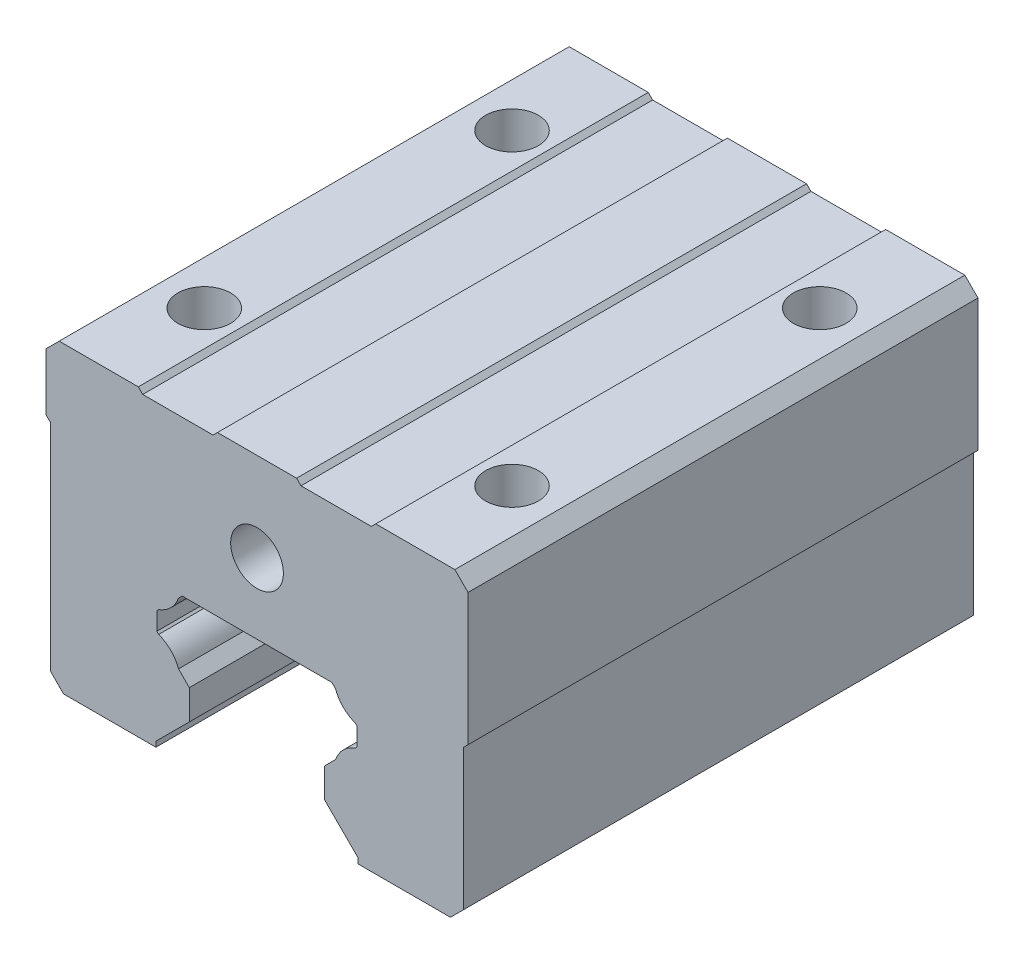
SolidWorks part; units mm, degrees
material "合金鋼"
ref_plane "Front Plane" through (0, 0, 0) normal (0, 0, 1) x (1, 0, 0)
ref_plane "Top Plane" through (0, 0, 0) normal (0, 1, 0) x (1, 0, 0)
ref_plane "Right Plane" through (0, 0, 0) normal (1, 0, 0) x (0, 0, -1)
sketch "Sketch2" plane through (0, 0, 0) normal (0, 0, 1) x (1, 0, 0)
  line L0 (22, 0) -> (23.5, 1.5)
  line L1 (23.5, 1.5) -> (23.5, 17.5)
  line L2 (23.5, 17.5) -> (24, 18)
  line L3 (24, 18) -> (24, 33)
  line L4 (24, 33) -> (22.5, 34.5)
  line L5 (22.5, 34.5) -> (13.5, 34.5)
  line L6 (13.5, 34.5) -> (13, 34)
  line L7 (13, 34) -> (5, 34)
  line L8 (5, 34) -> (4.5, 34.5)
  line L9 (4.5, 34.5) -> (-4.5, 34.5)
  line L10 (-4.5, 34.5) -> (-5, 34)
  line L11 (-5, 34) -> (-13, 34)
  line L12 (-13, 34) -> (-13.5, 34.5)
  line L13 (-13.5, 34.5) -> (-22.5, 34.5)
  line L14 (-22.5, 34.5) -> (-24, 33)
  line L15 (-24, 33) -> (-24, 26.5)
  line L16 (-24, 26.5) -> (-23.5, 26)
  line L17 (-23.5, 26) -> (-23.5, 1.5)
  line L18 (-23.5, 1.5) -> (-22, 0)
  line L19 (-7.7, 4.3937) -> (-11.5, 0.6)
  line L20 (-22, 0) -> (-11.5, 0)
  line L21 (11.5, 0) -> (22, 0)
  line L22 (-11.5, 0.6) -> (-11.5, 0)
  line L23 (7.7, 4.3937) -> (11.5, 0.6)
  line L24 (-7.7, 4.3937) -> (-7.7, 7.7737)
  line L25 (-7.7, 7.7737) -> (-8.93, 9.0057)
  line L26 (-11.1862, 11.2657) -> (-11.3959, 11.4757)
  line L27 (-11.3959, 11.4757) -> (-11.3959, 13.5057)
  line L28 (-11.3959, 13.5057) -> (-11.1862, 13.7157)
  line L29 (-8.93, 15.9757) -> (-8.5207, 16.3857)
  line L30 (-8.5207, 16.3857) -> (8.5207, 16.3857)
  line L31 (8.5207, 16.3857) -> (8.93, 15.9757)
  line L32 (11.1862, 13.7157) -> (11.3959, 13.5057)
  line L33 (11.3959, 13.5057) -> (11.3959, 11.4757)
  line L34 (11.3959, 11.4757) -> (11.1862, 11.2657)
  line L35 (8.93, 9.0057) -> (7.7, 7.7737)
  line L36 (7.7, 7.7737) -> (7.7, 4.3937)
  line L37 (11.5, 0.6) -> (11.5, 0)
  arc A0 (-8.93, 9.0057) -> (-11.1862, 11.2657) centre (-12.4594, 7.7384) ccw
  arc A1 (-11.1862, 13.7157) -> (-8.93, 15.9757) centre (-12.4594, 17.243) ccw
  arc A2 (8.93, 15.9757) -> (11.1862, 13.7157) centre (12.4594, 17.243) ccw
  arc A3 (11.1862, 11.2657) -> (8.93, 9.0057) centre (12.4594, 7.7384) ccw
  dimension "D10" = 1.5
  dimension "D9" = 3.8
  dimension "D28" = 34
  dimension "D11" = 0.6
  dimension "D19" = 2.26
  dimension "D1" = 34.5
  dimension "D2" = 6.5
  dimension "D4" = 9
  dimension "D5" = 15
  dimension "D6" = 0.6
  dimension "D7" = 8
  dimension "D8" = 9
  dimension "D12" = 0.5
  dimension "D13" = 3.7937
  dimension "D14" = 3.38
  dimension "D15" = 1.5
  dimension "D16" = 1.5
  dimension "D17" = 48
  dimension "D18" = 1.23
  dimension "D20" = 0.21
  dimension "D21" = 1.5
  dimension "D22" = 1.5
  dimension "D23" = 2.03
  dimension "D24" = 1.5
  dimension "D30" = 1.5
extrude "Block" add sketch "Sketch2" along normal mid plane 58
hole_wizard "Tap Drill for M8x1.0 Tap1" positions "Sketch6" profile "Sketch5" hole size "M8x1.0" standard "ANSI Metric"
sketch "Sketch6" plane through (0, 34.5, 0) normal (0, 1, 0) x (1, 0, 0)
  line L0 (-1000, 0) -> (49000, 0) construction
  line L1 (0, -1000) -> (0, 49000) construction
  point P0 (17.5, 17.5)
  point P2 (-17.5, 17.5)
  point P4 (17.5, -17.5)
  point P6 (-17.5, -17.5)
  dimension "D1" = 35
  dimension "D2" = 35
sketch "Sketch5" plane through (17.5, 34.5, -17.5) normal (1, 0, 0) x (0, 0, 1)
  line L0 (0, 0) -> (0, 14.0617)
  line L1 (0, 14.0617) -> (3, 12.5)
  line L2 (3, 12.5) -> (3, 0)
  line L5 (3, 0) -> (0, 0)
  line L10 (0, 14.0617) -> (-3, 12.5) construction
  line L11 (0, -6.35) -> (0, 107.95) construction
  dimension "Hole Dia." = 6
  dimension "Hole Depth" = 12.5
  dimension "Drill Angle" = 125
cosmetic thread "Cosmetic Thread1" parameters "D1"=10, "D2"=10
cosmetic thread "Cosmetic Thread2" parameters "D1"=10, "D2"=10
cosmetic thread "Cosmetic Thread3" parameters "D1"=10, "D2"=10
cosmetic thread "Cosmetic Thread4" parameters "D1"=10, "D2"=10
hole_wizard "Ø6.0 (6) Diameter Hole1" positions "Sketch9" profile "Sketch8" hole size "Ø6.0" standard "ANSI Metric" end condition through all
sketch "Sketch9" plane through (0, 0, -29) normal (0, 0, -1) x (-1, 0, 0)
  line L1 (8.5207, 16.3857) -> (-8.5207, 16.3857) construction
  point P0 (0, 24.3857)
  dimension "D1" = 8
sketch "Sketch8" plane through (0, 24.3857, -29) normal (1, 0, 0) x (0, 1, 0)
  line L0 (0, 0) -> (0, 58)
  line L1 (0, 58) -> (3, 58)
  line L2 (3, 58) -> (3, 0)
  line L5 (3, 0) -> (0, 0)
  line L11 (0, -6.35) -> (0, 107.95) construction
  dimension "Thru Hole Dia." = 6
  dimension "Thru Hole Depth" = 58
